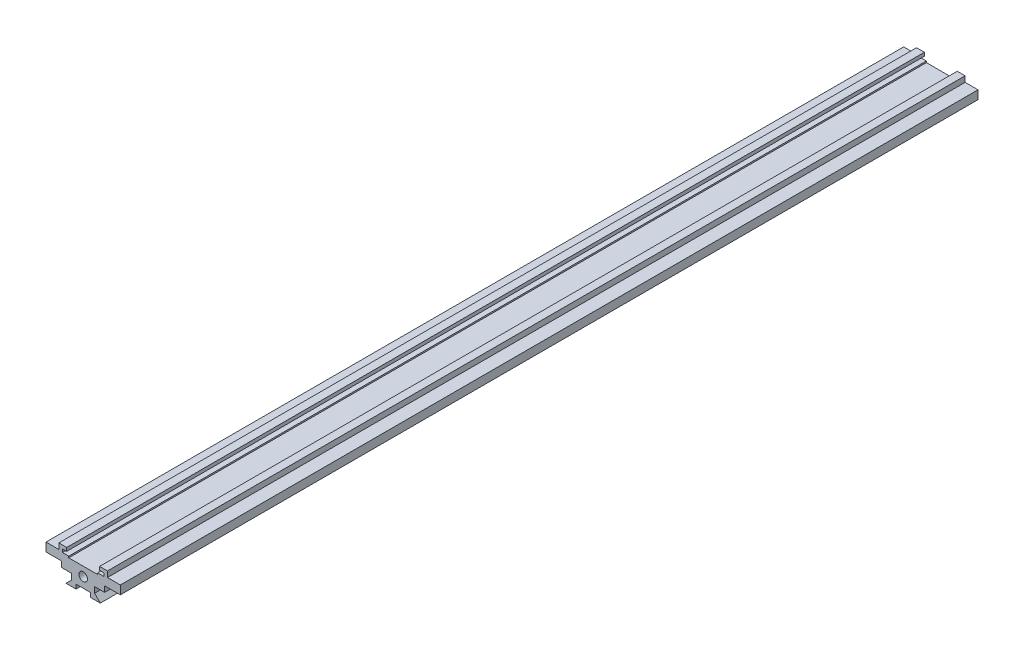
SolidWorks part; units mm, degrees
material "6061 合金"
ref_plane "前视基准面" through (0, 0, 0) normal (0, 0, 1) x (1, 0, 0)
ref_plane "上视基准面" through (0, 0, 0) normal (0, 1, 0) x (1, 0, 0)
ref_plane "右视基准面" through (0, 0, 0) normal (1, 0, 0) x (0, 0, -1)
sketch "草图1" plane through (0, 0, 0) normal (0, 0, 1) x (1, 0, 0)
  line L0 (13, 6) -> (7.5, 6)
  line L1 (-6, 0) -> (6, 0)
  line L2 (0, 0) -> (0, 8.2) construction
  line L3 (-4, 4) -> (-7.5, 4)
  line L4 (-8.5, 9) -> (-8.5, 11)
  line L5 (-8.5, 11) -> (-5.75, 11)
  line L6 (-5.75, 11) -> (-5.75, 9.8)
  line L7 (-4, 2) -> (-4, 4)
  line L8 (-6, 0) -> (-4, 2)
  line L9 (7.5, 4) -> (4, 4)
  line L10 (4, 2) -> (4, 4)
  line L11 (6, 0) -> (4, 2)
  line L12 (-5.75, 9.8) -> (-7.25, 9.8)
  line L13 (-7.25, 9.8) -> (-7.25, 8.7)
  line L14 (5.05, 8.2) -> (5.05, 8.7)
  line L15 (-8.5, 9) -> (-13, 9)
  line L16 (-7.5, 6) -> (-13, 6)
  line L17 (5.05, 8.7) -> (7.25, 8.7)
  line L18 (7.25, 9.8) -> (7.25, 8.7)
  line L19 (-13, 6) -> (-13, 9)
  line L20 (5.05, 8.2) -> (-5.05, 8.2)
  line L21 (-5.05, 8.7) -> (-7.25, 8.7)
  line L22 (8.5, 9) -> (13, 9)
  line L23 (5.75, 9.8) -> (7.25, 9.8)
  line L24 (5.75, 11) -> (5.75, 9.8)
  line L25 (8.5, 11) -> (5.75, 11)
  line L26 (-5.05, 8.2) -> (-5.05, 8.7)
  line L27 (8.5, 9) -> (8.5, 11)
  line L29 (13, 6) -> (13, 9)
  line L30 (-7.5, 4) -> (-7.5, 6)
  line L31 (7.5, 4) -> (7.5, 6)
  dimension "D2" = 90
  dimension "D3" = 11.5
  dimension "D4" = 12
  dimension "D5" = 8
  dimension "D6" = 17
  dimension "D7" = 15
  dimension "D8" = 2
  dimension "D9" = 26
  dimension "D10" = 14.5
  dimension "D11" = 10.1
  dimension "D12" = 4
  dimension "D13" = 3
  dimension "D14" = 2
  dimension "D15" = 0.5
  dimension "D16" = 1.1
  dimension "D17" = 1.2
extrude "凸台-拉伸1" add sketch "草图1" against normal mid plane 300
sketch "草图2" plane through (0, 0, -150) normal (0, 0, -1) x (-1, 0, 0)
  line L0 (-13, 9) -> (-8.5, 9) construction
  circle A0 centre (0, 5) radius 1.5
  dimension "D1" = 3
  dimension "D2" = 4
extrude "切除-拉伸1" cut sketch "草图2" against normal blind 6
sketch "草图4" plane through (0, 0, 150) normal (0, 0, 1) x (1, 0, 0)
  line L0 (-6, 0) -> (6, 0) construction
  line L1 (-2.5, 0) -> (2.5, 0)
  line L2 (-2.5, 0) -> (-2.5, 1.5)
  line L3 (-2.5, 1.5) -> (2.5, 1.5)
  line L4 (2.5, 0) -> (2.5, 1.5)
  dimension "D1" = 1.5
  dimension "D2" = 2.5
  dimension "D3" = 5
extrude "切除-拉伸3" cut sketch "草图4" against normal up to next
mirror "镜向1" about plane through (0, 0, 0) normal (0, 0, 1) of "切除-拉伸1"
